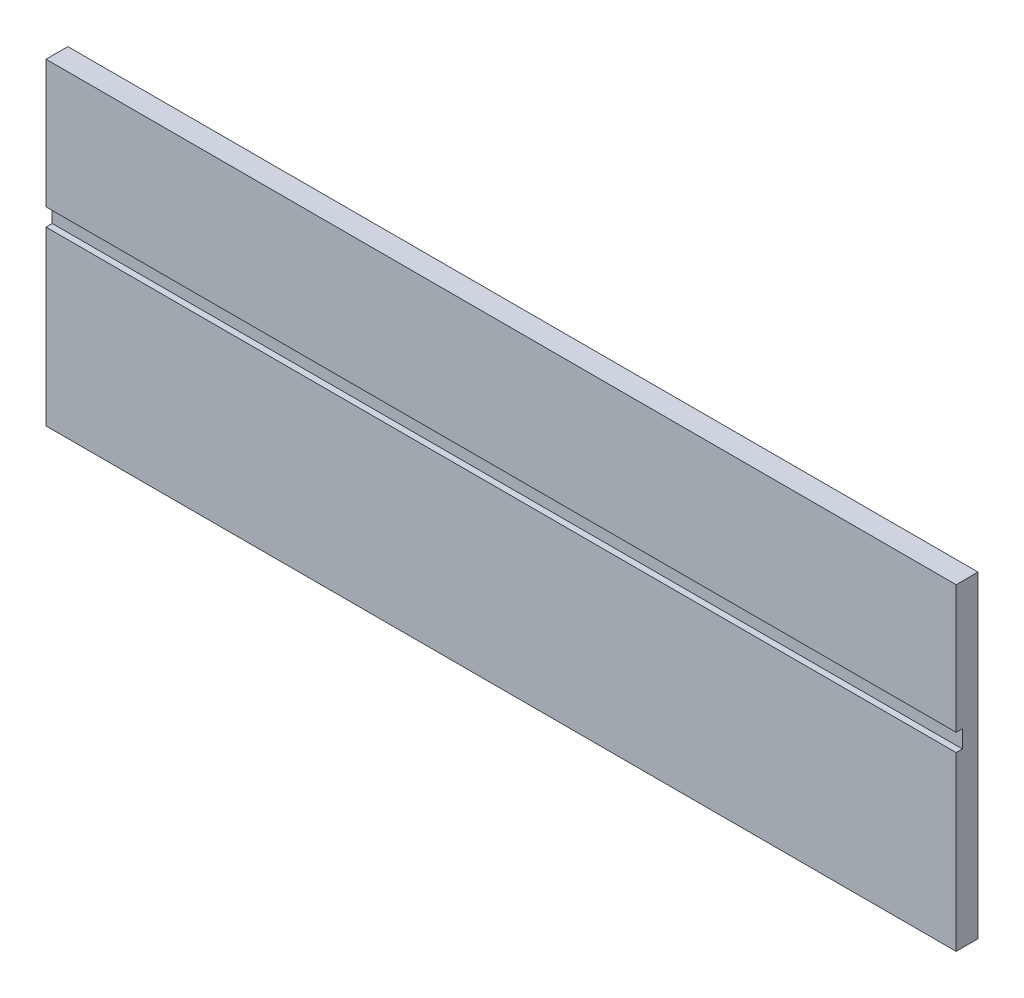
SolidWorks part; units mm, degrees
material "Pine"
ref_plane "Front Plane" through (0, 0, 0) normal (0, 0, 1) x (1, 0, 0)
ref_plane "Top Plane" through (0, 0, 0) normal (0, 1, 0) x (1, 0, 0)
ref_plane "Right Plane" through (0, 0, 0) normal (1, 0, 0) x (0, 0, -1)
sketch "Sketch1" plane through (0, 0, 0) normal (0, 0, 1) x (1, 0, 0)
  line L0 (-163.9887, -5335.905) -> (-163.9887, -5432.425)
  line L1 (-102.87, -5350.891) -> (-33.02, -5350.891)
  line L2 (-111.8235, -5341.9375) -> (-111.8235, -5334)
  line L3 (-24.0665, -5341.9375) -> (-24.0665, -5334)
  line L4 (-298.9262, -5332.73) -> (-167.1637, -5332.73)
  line L5 (-167.1637, -5435.6) -> (-298.9262, -5435.6)
  line L6 (-302.1012, -5432.425) -> (-302.1012, -5335.905)
  line L7 (-107.6325, -5329.809) -> (-28.2575, -5329.809)
  line L8 (174.9425, -5308.6) -> (174.9425, -5581.65)
  line L9 (449.2625, -5413.1661) -> (449.2625, -5421.9659)
  line L10 (595.3125, -5421.9659) -> (595.3125, -5413.1661)
  line L11 (839.47, -5509.5521) -> (839.47, -5307.6729)
  line L12 (839.47, -5307.6729) -> (863.6, -5307.6729)
  line L13 (839.47, -5509.5521) -> (863.6, -5509.5521)
  line L14 (863.6, -5509.5521) -> (863.6, -5307.6729)
  line L15 (-354.2665, -5341.9375) -> (-354.2665, -5334)
  line L16 (-100.8856, -5889.625) -> (-50.0856, -5889.625)
  line L17 (-104.0606, -5969) -> (-104.0606, -5892.8)
  line L18 (-46.9106, -5892.8) -> (-46.9106, -5969)
  line L19 (-50.0856, -5972.175) -> (-100.8856, -5972.175)
  line L20 (-100.8856, -5848.35) -> (-50.0856, -5848.35)
  line L21 (857.25, -5502.275) -> (157.1625, -5575.3)
  line L22 (857.25, -5314.95) -> (857.25, -5502.275)
  line L23 (157.1625, -5314.95) -> (157.1625, -5575.3)
  line L24 (857.25, -5314.95) -> (157.1625, -5314.95)
  line L25 (150.8125, -5308.6) -> (174.9425, -5308.6)
  line L26 (174.9425, -5581.65) -> (150.8125, -5581.65)
  line L27 (137.16, -5314.95) -> (137.16, -5502.275)
  line L28 (150.8125, -5581.65) -> (150.8125, -5308.6)
  line L29 (590.8224, -5408.676) -> (453.7526, -5408.676)
  line L30 (453.7526, -5426.456) -> (590.8224, -5426.456)
  line L31 (137.16, -6013.45) -> (137.16, -5867.4)
  line L32 (150.8125, -5746.75) -> (150.8125, -6019.8)
  line L33 (143.51, -5639.9938) -> (143.51, -5654.294)
  line L34 (590.8224, -5919.724) -> (453.7526, -5919.724)
  line L35 (453.7526, -5901.944) -> (590.8224, -5901.944)
  line L36 (449.2625, -5915.2339) -> (449.2625, -5906.4341)
  line L37 (174.9425, -6019.8) -> (174.9425, -5746.75)
  line L38 (595.3125, -5906.4341) -> (595.3125, -5915.2339)
  line L39 (839.47, -5818.8479) -> (839.47, -6020.7271)
  line L40 (839.47, -5818.8479) -> (863.6, -5818.8479)
  line L41 (863.6, -5818.8479) -> (863.6, -6020.7271)
  line L42 (839.47, -6020.7271) -> (863.6, -6020.7271)
  line L43 (-155.8782, -5867.4) -> (-603.25, -5867.4)
  line L44 (-433.07, -5350.891) -> (-363.22, -5350.891)
  line L45 (-437.8325, -5329.809) -> (-358.4575, -5329.809)
  line L46 (889, -6045.2) -> (-635, -6045.2)
  line L47 (-635, -5283.2) -> (889, -5283.2)
  line L48 (-635, -6045.2) -> (-635, -5283.2)
  line L49 (889, -5283.2) -> (889, -6045.2)
  line L50 (137.16, -5502.275) -> (-603.25, -5502.275)
  line L51 (-603.25, -5314.95) -> (137.16, -5314.95)
  line L52 (143.51, -5654.294) -> (-609.6, -5654.294)
  line L53 (-609.6, -5639.9938) -> (143.51, -5639.9938)
  line L54 (137.16, -5536.0062) -> (-603.25, -5536.0062)
  line L55 (-603.25, -5794.375) -> (137.16, -5794.375)
  line L56 (-603.25, -6013.45) -> (137.16, -6013.45)
  line L57 (-603.25, -5536.0062) -> (-603.25, -5794.375)
  line L58 (137.16, -5794.375) -> (137.16, -5536.0062)
  line L59 (-609.6, -5654.294) -> (-609.6, -5639.9938)
  line L60 (-603.25, -5867.4) -> (-603.25, -6013.45)
  line L61 (-603.25, -5314.95) -> (-603.25, -5502.275)
  line L62 (-442.0235, -5341.9375) -> (-442.0235, -5334)
  line L63 (857.25, -5826.125) -> (157.1625, -5753.1)
  line L64 (857.25, -6013.45) -> (857.25, -5826.125)
  line L65 (157.1625, -6013.45) -> (157.1625, -5753.1)
  line L66 (857.25, -6013.45) -> (157.1625, -6013.45)
  line L67 (174.9425, -5746.75) -> (150.8125, -5746.75)
  line L68 (150.8125, -6019.8) -> (174.9425, -6019.8)
  line L69 (137.16, -5867.4) -> (4.907, -5867.4)
  circle A0 centre (-36.195, -5484.0124) radius 1.5875
  arc A1 (-298.9262, -5332.73) -> (-302.1012, -5335.905) centre (-298.9262, -5335.905) ccw
  arc A2 (-302.1012, -5432.425) -> (-298.9262, -5435.6) centre (-298.9262, -5432.425) ccw
  arc A3 (-163.9887, -5335.905) -> (-167.1637, -5332.73) centre (-167.1637, -5335.905) ccw
  arc A4 (-167.1637, -5435.6) -> (-163.9887, -5432.425) centre (-167.1637, -5432.425) ccw
  arc A5 (-111.8235, -5341.9375) -> (-102.87, -5350.891) centre (-102.87, -5341.9375) ccw
  arc A6 (-107.6325, -5329.809) -> (-111.8235, -5334) centre (-107.6325, -5334) ccw
  circle A7 centre (166.0525, -5444.6613) radius 1.5875
  circle A8 centre (166.0525, -5358.1871) radius 1.5875
  circle A9 centre (471.4875, -5417.566) radius 1.5875
  arc A10 (453.7526, -5408.676) -> (449.2625, -5413.1661) centre (451.5076, -5410.9211) ccw
  arc A11 (449.2625, -5421.9659) -> (453.7526, -5426.456) centre (451.5076, -5424.2109) ccw
  circle A12 centre (522.2875, -5417.566) radius 1.5875
  circle A13 centre (573.0875, -5417.566) radius 1.5875
  arc A14 (590.8224, -5426.456) -> (595.3125, -5421.9659) centre (593.0674, -5424.2109) ccw
  arc A15 (595.3125, -5413.1661) -> (590.8224, -5408.676) centre (593.0674, -5410.9211) ccw
  circle A16 centre (848.36, -5471.8269) radius 1.5875
  circle A17 centre (848.36, -5409.0762) radius 1.5875
  circle A18 centre (848.36, -5346.3254) radius 1.5875
  arc A19 (-363.22, -5350.891) -> (-354.2665, -5341.9375) centre (-363.22, -5341.9375) ccw
  arc A20 (-354.2665, -5334) -> (-358.4575, -5329.809) centre (-358.4575, -5334) ccw
  arc A21 (-24.0665, -5334) -> (-28.2575, -5329.809) centre (-28.2575, -5334) ccw
  arc A22 (-33.02, -5350.891) -> (-24.0665, -5341.9375) centre (-33.02, -5341.9375) ccw
  circle A23 centre (-86.995, -5484.0124) radius 1.5875
  circle A24 centre (-333.4544, -5894.07) radius 2.54
  circle A25 centre (-333.4544, -5994.4) radius 2.54
  arc A26 (-104.0606, -5969) -> (-100.8856, -5972.175) centre (-100.8856, -5969) ccw
  arc A27 (-50.0856, -5972.175) -> (-46.9106, -5969) centre (-50.0856, -5969) ccw
  arc A28 (-100.8856, -5848.35) -> (-128.3819, -5857.875) centre (-100.8856, -5892.8) ccw
  arc A29 (-155.8782, -5867.4) -> (-128.3819, -5857.875) centre (-155.8782, -5822.95) ccw
  arc A30 (-22.5893, -5857.875) -> (-50.0856, -5848.35) centre (-50.0856, -5892.8) ccw
  circle A31 centre (-132.6356, -5894.07) radius 2.54
  circle A32 centre (-132.6356, -5994.4) radius 2.54
  arc A33 (-46.9106, -5892.8) -> (-50.0856, -5889.625) centre (-50.0856, -5892.8) ccw
  arc A34 (-100.8856, -5889.625) -> (-104.0606, -5892.8) centre (-100.8856, -5892.8) ccw
  arc A35 (-22.5893, -5857.875) -> (4.907, -5867.4) centre (4.907, -5822.95) ccw
  circle A36 centre (166.0525, -5531.1356) radius 1.5875
  arc A37 (449.2625, -5915.2339) -> (453.7526, -5919.724) centre (451.5076, -5917.4789) ccw
  arc A38 (453.7526, -5901.944) -> (449.2625, -5906.4341) centre (451.5076, -5904.1891) ccw
  circle A39 centre (166.0525, -5797.2644) radius 1.5875
  circle A40 centre (166.0525, -5883.7387) radius 1.5875
  circle A41 centre (166.0525, -5970.2129) radius 1.5875
  circle A42 centre (471.4875, -5910.834) radius 1.5875
  circle A43 centre (522.2875, -5910.834) radius 1.5875
  circle A44 centre (573.0875, -5910.834) radius 1.5875
  arc A45 (595.3125, -5906.4341) -> (590.8224, -5901.944) centre (593.0674, -5904.1891) ccw
  arc A46 (590.8224, -5919.724) -> (595.3125, -5915.2339) centre (593.0674, -5917.4789) ccw
  circle A47 centre (848.36, -5919.3238) radius 1.5875
  circle A48 centre (848.36, -5982.0746) radius 1.5875
  circle A49 centre (848.36, -5856.5731) radius 1.5875
  arc A50 (-437.8325, -5329.809) -> (-442.0235, -5334) centre (-437.8325, -5334) ccw
  circle A51 centre (-429.895, -5484.0124) radius 1.5875
  arc A52 (-442.0235, -5341.9375) -> (-433.07, -5350.891) centre (-433.07, -5341.9375) ccw
  circle A53 centre (-379.095, -5484.0124) radius 1.5875
sketch "HeadTopOutline" plane through (0, 0, 0) normal (0, 0, 1) x (1, 0, 0)
  line L0 (137.16, -5794.375) -> (137.16, -5536.0062)
  line L1 (137.16, -5536.0062) -> (-603.25, -5536.0062)
  line L2 (-603.25, -5536.0062) -> (-603.25, -5794.375)
  line L3 (-603.25, -5794.375) -> (137.16, -5794.375)
  line L4 (-233.045, -5794.375) -> (-233.045, -5536.0062) construction
  line L5 (-603.25, -5665.1906) -> (-233.045, -5665.1906) construction
  line L6 (137.16, -5665.1906) -> (-233.045, -5665.1906) construction
  dimension "Width" = 258.3688
  dimension "Length" = 740.41
extrude "HeadTopOutline_Thickness" add sketch "HeadTopOutline" against normal blind 17.78
sketch "HeadTop_DisplaySlot" plane through (0, 0, 0) normal (0, 0, 1) x (1, 0, 0)
  line L0 (-603.25, -5639.9938) -> (137.16, -5639.9938)
  line L1 (-609.6, -5639.9938) -> (143.51, -5639.9938) construction
  line L2 (-603.25, -5536.0062) -> (-603.25, -5794.375) construction
  line L3 (137.16, -5794.375) -> (137.16, -5536.0062) construction
  line L4 (137.16, -5639.9938) -> (137.16, -5654.294)
  line L5 (143.51, -5654.294) -> (-609.6, -5654.294) construction
  line L6 (137.16, -5654.294) -> (-603.25, -5654.294)
  line L7 (-603.25, -5654.294) -> (-603.25, -5639.9938)
extrude "HeadTop_DisplaySlot_Depth" cut sketch "HeadTop_DisplaySlot" against normal blind 5.08
